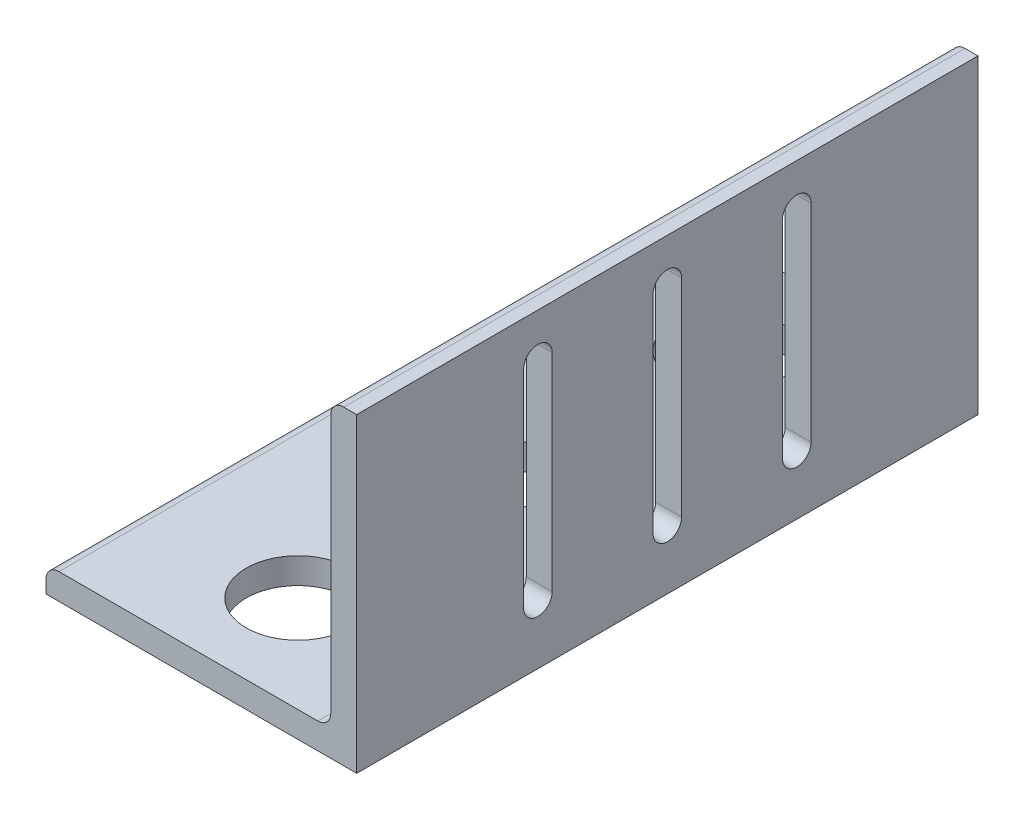
SolidWorks part; units mm, degrees
ref_plane "Front Plane" through (0, 0, 0) normal (0, 0, 1) x (1, 0, 0)
ref_plane "Top Plane" through (0, 0, 0) normal (0, 1, 0) x (1, 0, 0)
ref_plane "Right Plane" through (0, 0, 0) normal (1, 0, 0) x (0, 0, -1)
sketch "Sketch2" plane through (0, 0, 0) normal (0, 0, 1) x (1, 0, 0)
  line L0 (-38.1, 0) -> (38.1, 0)
  line L1 (38.1, 0) -> (38.1, 76.2)
  line L2 (38.1, 76.2) -> (31.75, 76.2) construction
  line L3 (31.75, 73.025) -> (31.75, 9.525)
  line L4 (28.575, 6.35) -> (-34.925, 6.35)
  line L5 (-38.1, 0) -> (-38.1, 6.35) construction
  line L6 (34.925, 76.2) -> (38.1, 76.2)
  line L7 (-38.1, 3.175) -> (-38.1, 0)
  arc A0 (31.75, 73.025) -> (34.925, 76.2) centre (34.925, 73.025) cw
  arc A1 (-38.1, 3.175) -> (-34.925, 6.35) centre (-34.925, 3.175) cw
  arc A2 (31.75, 9.525) -> (28.575, 6.35) centre (28.575, 9.525) cw
  dimension "Vert" = 76.2
  dimension "Horz" = 76.2
  dimension "Thickness" = 6.35
extrude "Boss-Extrude1" add sketch "Sketch2" along normal mid plane 152.4
ref_plane "Contact Plane 1" through (0, 6.35, 0) normal (0, 1, 0) x (1, 0, 0)
ref_plane "Contact Plane 2" through (31.75, 0, 0) normal (-1, 0, 0) x (0, 0, 1)
sketch "Sketch3" plane through (38.1, 0, 0) normal (1, 0, 0) x (0, 0, -1)
  line L0 (-31.75, 65.4) -> (-31.75, 14.6) construction
  line L1 (-28.25, 65.4) -> (-28.25, 14.6)
  line L2 (-35.25, 65.4) -> (-35.25, 14.6)
  line L3 (0, 0) -> (0, 76.2) construction
  line L4 (-76.2, 0) -> (76.2, 0) construction
  line L5 (-76.2, 76.2) -> (76.2, 76.2) construction
  line L6 (31.75, 65.4) -> (31.75, 14.6) construction
  line L7 (28.25, 65.4) -> (28.25, 14.6)
  line L8 (35.25, 65.4) -> (35.25, 14.6)
  line L9 (0, 65.4) -> (0, 14.6) construction
  line L10 (3.5, 65.4) -> (3.5, 14.6)
  line L11 (-3.5, 65.4) -> (-3.5, 14.6)
  arc A0 (-28.25, 65.4) -> (-35.25, 65.4) centre (-31.75, 65.4) ccw
  arc A1 (-35.25, 14.6) -> (-28.25, 14.6) centre (-31.75, 14.6) ccw
  arc A2 (28.25, 65.4) -> (35.25, 65.4) centre (31.75, 65.4) cw
  arc A3 (35.25, 14.6) -> (28.25, 14.6) centre (31.75, 14.6) cw
  arc A4 (3.5, 65.4) -> (-3.5, 65.4) centre (0, 65.4) ccw
  arc A5 (-3.5, 14.6) -> (3.5, 14.6) centre (0, 14.6) ccw
  point P2 (-31.75, 40)
  point P15 (31.75, 40)
  point P22 (0, 40)
  dimension "D1" = 3.5
  dimension "D3" = 31.75
  dimension "D5" = 3.5
  dimension "D2" = 50.8
  dimension "D4" = 40
  dimension "D6" = 50.8
extrude "Cut-Extrude1" cut sketch "Sketch3" against normal blind 10
sketch "Sketch4" plane through (0, 0, 0) normal (0, -1, 0) x (1, 0, 0)
  line L0 (-38.1, 76.2) -> (-38.1, -76.2) construction
  circle A2 centre (0, 0) radius 10
  circle A3 centre (0, 52.5) radius 12.7
  circle A4 centre (0, -52.5) radius 12.7
  dimension "D1" = 38.1
  dimension "D3" = 20
  dimension "D6" = 25.4
  dimension "D7" = 52.5
  dimension "D2" = 38.1
  dimension "D8" = 52.5
extrude "Cut-Extrude2" cut sketch "Sketch4" against normal blind 10
